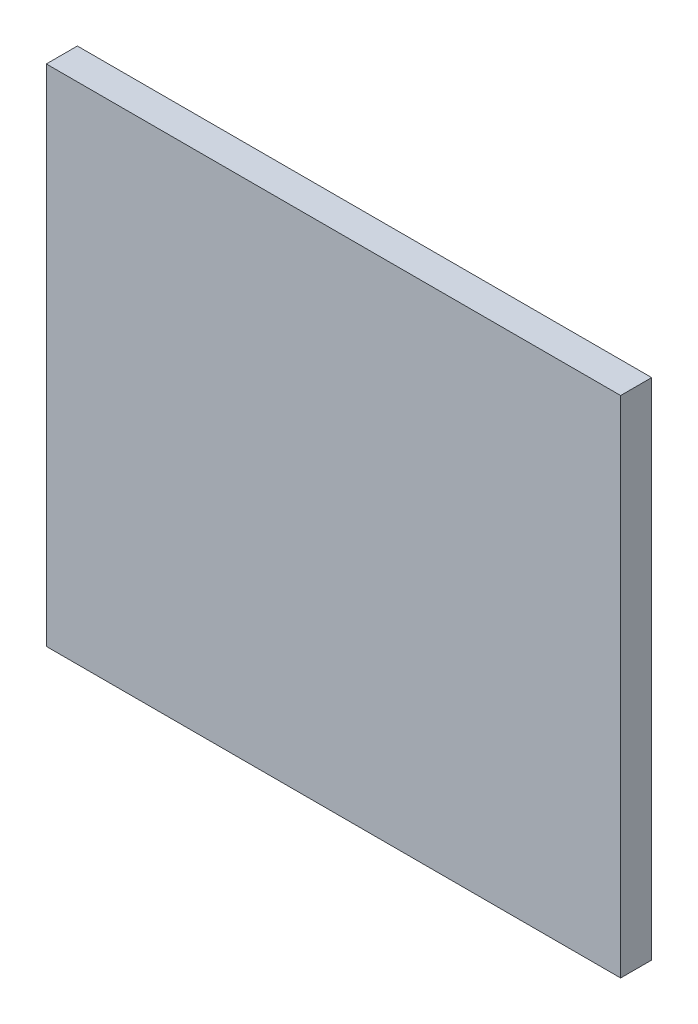
SolidWorks part; units mm, degrees
material "Maple"
ref_plane "Front Plane" through (0, 0, 0) normal (0, 0, 1) x (1, 0, 0)
ref_plane "Top Plane" through (0, 0, 0) normal (0, 1, 0) x (1, 0, 0)
ref_plane "Right Plane" through (0, 0, 0) normal (1, 0, 0) x (0, 0, -1)
sketch "Sketch1" plane through (0, 0, 0) normal (0, 0, 1) x (1, 0, 0)
  line L1 (-37, -32.5) -> (37, -32.5)
  line L2 (-37, -32.5) -> (-37, 32.5)
  line L3 (-37, 32.5) -> (37, 32.5)
  line L4 (37, -32.5) -> (37, 32.5)
  line L5 (-37, -32.5) -> (37, 32.5) construction
  line L6 (-37, 32.5) -> (37, -32.5) construction
  point P0 (0, 0)
  dimension "D1" = 65
  dimension "D2" = 74
extrude "Boss-Extrude1" add sketch "Sketch1" along normal blind 4
